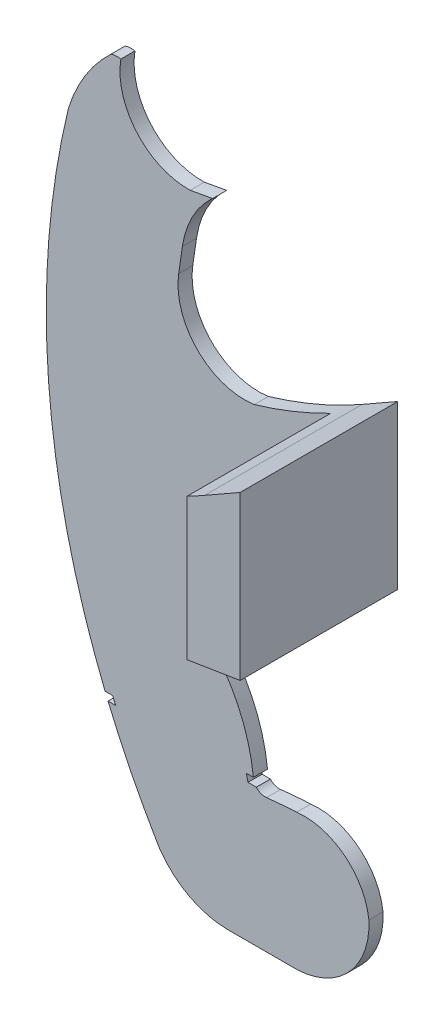
SolidWorks part; units mm, degrees
ref_plane "Front Plane" through (0, 0, 0) normal (0, 0, 1) x (1, 0, 0)
ref_plane "Top Plane" through (0, 0, 0) normal (0, 1, 0) x (1, 0, 0)
ref_plane "Right Plane" through (0, 0, 0) normal (1, 0, 0) x (0, 0, -1)
sketch "Sketch1" plane through (0, 0, 0) normal (0, 0, 1) x (1, 0, 0)
  line L11 (13.2754, 31.2051) -> (14.8981, 31.2007)
  line L34 (45.4286, 29.6189) -> (43.6642, 29.6237)
  line L35 (39.4326, 0.3496) -> (54.167, 0.3496)
  line L36 (15.525, 29.699) -> (13.8957, 29.7034)
  line L50 (49.9064, 74.3999) -> (72.499, 78.0472)
  line L51 (44.7935, 73.6221) -> (49.9064, 74.3999)
  line L52 (43.3052, 31.1246) -> (44.8147, 31.1206)
  line L134 (15.525, 29.699) -> (14.8981, 31.2007)
  line L135 (43.3052, 31.1246) -> (43.6642, 29.6237)
  line L140 (36.1401, 133.3588) -> (31.3861, 132.4985)
  line L141 (28.925, 115.9215) -> (29.7123, 121.31)
  line L144 (72.499, 112.6667) -> (64.966, 108.3712)
  line L145 (72.499, 78.0472) -> (72.499, 112.6667)
  arc A0 (44.9744, 99.8363) -> (64.966, 108.3712) centre (17.9374, 190.8466) ccw
  arc A27 (9.194, 142.6821) -> (5.4736, 134.6098) centre (37.4024, 124.7876) ccw
  arc A28 (5.4736, 134.6098) -> (13.2754, 31.2051) centre (169.8716, 95.0168) ccw
  arc A29 (14.5345, 149.1389) -> (9.194, 142.6821) centre (37.4024, 124.7876) ccw
  arc A79 (45.4286, 29.6189) -> (47.5925, 28.7766) centre (47.3137, 31.261) ccw
  arc A80 (54.0043, 29.2989) -> (47.5925, 28.7766) centre (59.3599, -76.0788) ccw
  arc A81 (69.3675, 17.1504) -> (54.0043, 29.2989) centre (55.6114, 15.5427) ccw
  arc A82 (54.167, 0.3496) -> (69.3675, 17.1504) centre (53.4145, 16.3071) ccw
  arc A83 (25.2539, 7.5014) -> (39.4326, 0.3496) centre (39.4326, 17.9802) ccw
  arc A84 (24.5053, 8.6283) -> (25.2539, 7.5014) centre (36.1107, 15.5252) ccw
  arc A85 (13.8957, 29.7034) -> (24.5053, 8.6283) centre (169.8717, 95.0167) ccw
  arc A105 (44.7935, 73.6221) -> (38.5654, 71.8208) centre (60.4439, 7.8433) ccw
  arc A106 (38.5654, 71.8208) -> (35.0752, 69.3586) centre (40.7988, 64.9501) ccw
  arc A107 (35.0752, 69.3586) -> (34.3739, 52.8389) centre (44.7935, 60.6713) ccw
  arc A108 (44.8147, 31.1206) -> (34.3739, 52.8389) centre (9.0237, 27.2834) ccw
  arc A164 (16.6271, 149.2816) -> (14.5345, 149.1389) centre (15.831, 145.5415) ccw
  arc A165 (16.6271, 149.2816) -> (31.3861, 132.4985) centre (30.9452, 146.9918) ccw
  arc A166 (35.7831, 133.0506) -> (36.1401, 133.3588) centre (30.9663, 138.9898) ccw
  arc A167 (35.7831, 133.0506) -> (34.324, 131.5058) centre (49.7675, 118.3798) ccw
  arc A168 (34.324, 131.5058) -> (34.0415, 131.1661) centre (49.7675, 118.3798) ccw
  arc A169 (34.0415, 131.1661) -> (29.7123, 121.31) centre (49.7675, 118.3798) ccw
  arc A170 (28.925, 115.9215) -> (44.9744, 99.8363) centre (42.9556, 113.8715) ccw
extrude "Boss-Extrude2" add sketch "Sketch1" along normal blind 3
sketch "Sketch2" plane through (0, 0, 3) normal (0, 0, 1) x (1, 0, 0)
  line L8 (61.2367, 76.229) -> (61.2367, 106.3538)
  line L9 (49.9064, 74.3999) -> (72.499, 78.0472)
  line L10 (72.499, 112.6667) -> (64.966, 108.3712)
  line L11 (72.499, 78.0472) -> (72.499, 112.6667)
  line L12 (61.2367, 76.229) -> (72.499, 78.0472)
  line L14 (72.499, 78.0472) -> (72.499, 112.6667)
  line L15 (64.966, 108.3712) -> (72.499, 112.6667)
  line L16 (64.966, 108.3712) -> (72.499, 112.6667)
  arc A3 (44.9744, 99.8363) -> (64.966, 108.3712) centre (17.9374, 190.8466) ccw
  arc A4 (61.2367, 106.3538) -> (64.966, 108.3712) centre (17.9374, 190.8466) ccw
  dimension "D1" = 0
  dimension "D2" = 0
extrude "Boss-Extrude3" add sketch "Sketch2" along normal blind 30.5
ref_plane "Plane1" through (0, 0, 13) normal (0, 0, 1) x (1, 0, 0)
sketch "Sketch7" plane through (0, 0, 13) normal (0, 0, 1) x (1, 0, 0)
  line L32 (37.9207, 123.5186) -> (32.5302, 122.5431)
  line L33 (61.2367, 86.3585) -> (61.2367, 95.2544)
  line L46 (19.8174, 122.7557) -> (19.0301, 117.3672)
  line L47 (19.8174, 122.7557) -> (19.0301, 117.3672)
  line L70 (42.8951, 83.4484) -> (48.3575, 84.2793)
  line L71 (48.3575, 84.2793) -> (59.643, 86.1012)
  line L72 (42.8951, 83.4484) -> (48.3575, 84.2793)
  line L73 (48.3575, 84.2793) -> (59.643, 86.1012)
  line L76 (22.536, 34.9787) -> (23.1197, 33.5658)
  line L77 (53.8745, 10.3496) -> (39.4326, 10.3496)
  line L78 (53.8745, 10.3496) -> (39.4326, 10.3496)
  line L79 (59.643, 86.1012) -> (61.2367, 86.3585)
  arc A79 (14.4232, 128.9011) -> (32.5302, 122.5431) centre (30.9452, 146.9918) ccw
  arc A80 (14.4232, 128.9011) -> (22.536, 34.9787) centre (169.8716, 95.0168) ccw
  arc A81 (14.4232, 128.9011) -> (20.2238, 124.9622) centre (30.9452, 146.9918) ccw
  arc A82 (14.4232, 128.9011) -> (22.536, 34.9787) centre (169.8716, 95.0168) ccw
  arc A100 (47.1971, 90.0668) -> (65.7974, 97.4543) centre (17.9374, 190.8466) ccw
  arc A101 (19.0301, 117.3672) -> (47.1971, 90.0668) centre (42.9556, 113.8715) ccw
  arc A102 (28.8834, 140.2889) -> (19.8174, 122.7557) centre (49.7675, 118.3798) ccw
  arc A103 (47.1971, 90.0668) -> (61.2367, 95.2544) centre (17.9374, 190.8466) ccw
  arc A104 (19.0301, 117.3672) -> (47.1971, 90.0668) centre (42.9556, 113.8715) ccw
  arc A105 (20.2238, 124.9622) -> (19.8174, 122.7557) centre (49.7675, 118.3798) ccw
  arc A118 (34.8716, 30.0546) -> (26.9255, 46.1334) centre (9.0237, 27.2834) ccw
  arc A119 (42.8951, 83.4484) -> (35.3886, 81.303) centre (60.4439, 7.8433) ccw
  arc A120 (27.3962, 75.7693) -> (26.9255, 46.1334) centre (44.7935, 60.6713) ccw
  arc A121 (35.3886, 81.303) -> (27.3962, 75.7693) centre (40.7988, 64.9501) ccw
  arc A122 (34.8716, 30.0546) -> (26.9255, 46.1334) centre (9.0237, 27.2834) ccw
  arc A123 (42.8951, 83.4484) -> (35.3886, 81.303) centre (60.4439, 7.8433) ccw
  arc A124 (27.3962, 75.7693) -> (26.9255, 46.1334) centre (44.7935, 60.6713) ccw
  arc A125 (35.3886, 81.303) -> (27.3962, 75.7693) centre (40.7988, 64.9501) ccw
  arc A154 (34.8716, 30.0546) -> (37.8883, 23.0506) centre (47.3155, 31.2626) ccw
  arc A161 (33.1019, 13.7371) -> (33.2959, 13.4449) centre (36.1107, 15.5252) ccw
  arc A162 (23.1197, 33.5658) -> (33.1019, 13.7371) centre (169.8717, 95.0167) ccw
  arc A163 (33.2959, 13.4449) -> (39.4326, 10.3496) centre (39.4326, 17.9802) ccw
  arc A164 (53.8745, 10.3496) -> (59.3897, 16.2808) centre (53.4145, 16.3071) ccw
  arc A165 (59.3897, 16.2808) -> (54.9334, 19.3322) centre (55.6114, 15.5427) ccw
  arc A166 (54.9334, 19.3322) -> (48.7078, 18.839) centre (59.3599, -76.0788) ccw
  arc A167 (37.8883, 23.0506) -> (48.7078, 18.839) centre (47.3137, 31.261) ccw
  arc A168 (33.1019, 13.7371) -> (33.2959, 13.4449) centre (36.1107, 15.5252) ccw
  arc A169 (23.1197, 33.5658) -> (33.1019, 13.7371) centre (169.8717, 95.0167) ccw
  arc A170 (33.2959, 13.4449) -> (39.4326, 10.3496) centre (39.4326, 17.9802) ccw
  arc A171 (53.8745, 10.3496) -> (59.3897, 16.2808) centre (53.4145, 16.3071) ccw
  arc A172 (59.3897, 16.2808) -> (54.9334, 19.3322) centre (55.6114, 15.5427) ccw
  arc A173 (54.9334, 19.3322) -> (48.7078, 18.839) centre (59.3599, -76.0788) ccw
  arc A174 (37.8883, 23.0506) -> (48.7078, 18.839) centre (47.3137, 31.261) ccw
  dimension "D1" = 10
  dimension "D2" = 10
  dimension "D3" = 10
  dimension "D4" = 10
sketch "Sketch8" plane through (0, 0, 3) normal (0, 0, 1) x (1, 0, 0)
  line L15 (49.9064, 74.3999) -> (44.7935, 73.6221)
  line L16 (61.2367, 76.229) -> (49.9064, 74.3999)
  line L20 (13.2754, 31.2051) -> (13.8957, 29.7034)
  line L26 (28.925, 115.9215) -> (29.7123, 121.31)
  line L27 (36.1401, 133.3588) -> (31.3861, 132.4985)
  line L38 (39.4326, 0.3496) -> (54.167, 0.3496)
  line L40 (45.4286, 29.6189) -> (44.8147, 31.1206)
  line L45 (61.2367, 106.3538) -> (61.2367, 76.229)
  arc A17 (44.8147, 31.1206) -> (34.3739, 52.8389) centre (9.0237, 27.2834) ccw
  arc A18 (35.0752, 69.3586) -> (34.3739, 52.8389) centre (44.7935, 60.6713) ccw
  arc A19 (38.5654, 71.8208) -> (35.0752, 69.3586) centre (40.7988, 64.9501) ccw
  arc A20 (44.7935, 73.6221) -> (38.5654, 71.8208) centre (60.4439, 7.8433) ccw
  arc A50 (45.4286, 29.6189) -> (47.5925, 28.7766) centre (47.3137, 31.261) ccw
  arc A59 (24.5053, 8.6283) -> (25.2539, 7.5014) centre (36.1107, 15.5252) ccw
  arc A60 (13.8957, 29.7034) -> (24.5053, 8.6283) centre (169.8717, 95.0167) ccw
  arc A61 (25.2539, 7.5014) -> (39.4326, 0.3496) centre (39.4326, 17.9802) ccw
  arc A62 (54.167, 0.3496) -> (69.3675, 17.1504) centre (53.4145, 16.3071) ccw
  arc A63 (69.3675, 17.1504) -> (54.0043, 29.2989) centre (55.6114, 15.5427) ccw
  arc A64 (54.0043, 29.2989) -> (47.5925, 28.7766) centre (59.3599, -76.0788) ccw
  arc A73 (44.9744, 99.8363) -> (61.2367, 106.3538) centre (17.9374, 190.8466) ccw
  arc A85 (28.925, 115.9215) -> (44.9744, 99.8363) centre (42.9556, 113.8715) ccw
  arc A86 (35.7831, 133.0506) -> (29.7123, 121.31) centre (49.7675, 118.3798) ccw
  arc A87 (35.7831, 133.0506) -> (36.1401, 133.3588) centre (30.9663, 138.9898) ccw
  arc A88 (16.6271, 149.2816) -> (31.3861, 132.4985) centre (30.9452, 146.9918) ccw
  arc A89 (14.5345, 149.1389) -> (5.4736, 134.6098) centre (37.4024, 124.7876) ccw
  arc A90 (16.6271, 149.2816) -> (14.5345, 149.1389) centre (15.831, 145.5415) ccw
  arc A91 (5.4736, 134.6098) -> (13.2754, 31.2051) centre (169.8716, 95.0168) ccw
  point P0 (0, 0)
  point P12 (-12.7023, 27.2834)
